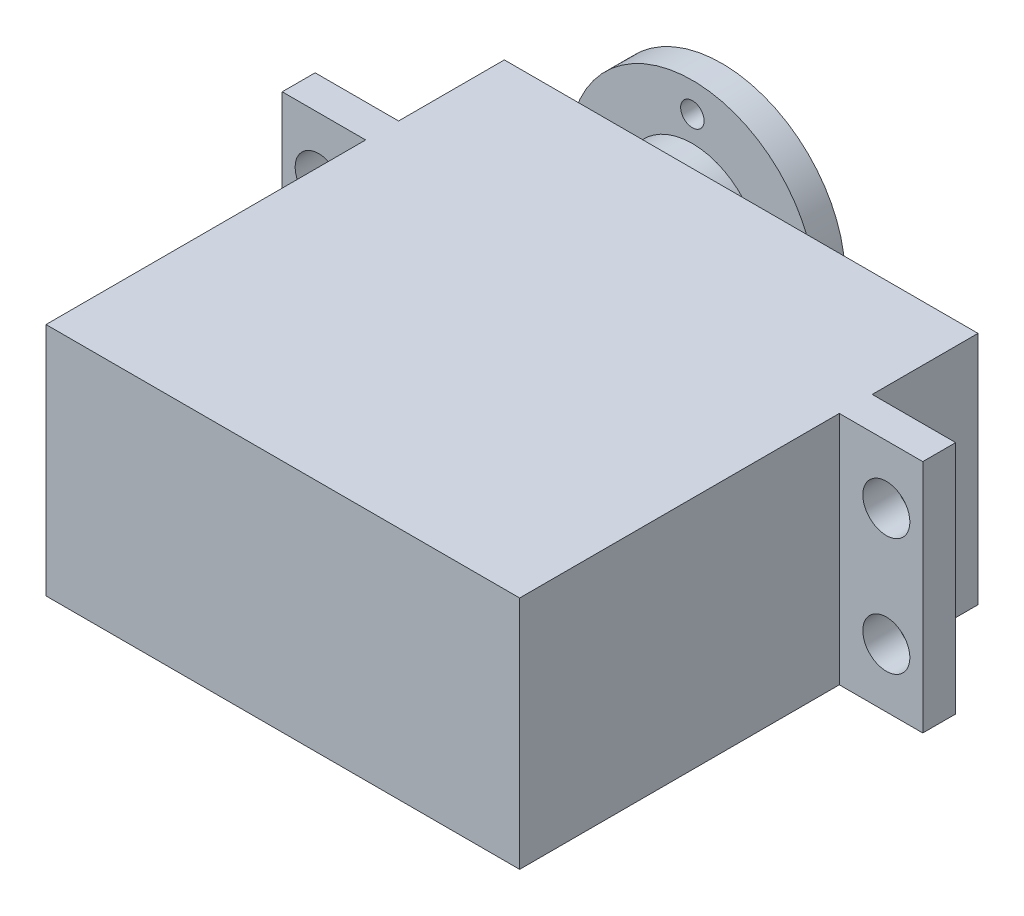
SolidWorks part; units mm, degrees
ref_plane "Alzado" through (0, 0, 0) normal (0, 0, 1) x (1, 0, 0)
ref_plane "Planta" through (0, 0, 0) normal (0, 1, 0) x (1, 0, 0)
ref_plane "Vista lateral" through (0, 0, 0) normal (1, 0, 0) x (0, 0, -1)
sketch "Croquis1" plane through (0, 0, 0) normal (0, 1, 0) x (1, 0, 0)
  line L0 (0, 19.5) -> (0, -19.5) construction
  line L1 (20.15, 19.5) -> (-20.15, 19.5)
  line L2 (20.15, -19.5) -> (20.15, 7.7)
  line L3 (20.15, -19.5) -> (-20.15, -19.5)
  line L4 (-20.15, -19.5) -> (-20.15, 7.7)
  line L5 (20.15, 19.5) -> (-20.15, -19.5) construction
  line L6 (20.15, -19.5) -> (-20.15, 19.5) construction
  line L7 (-20.15, 10.5) -> (-20.15, 19.5)
  line L8 (-20.15, 10.5) -> (-27.25, 10.5)
  line L9 (20.15, 10.5) -> (20.15, 19.5)
  line L10 (-20.15, 7.7) -> (-27.25, 7.7)
  line L11 (-27.25, 10.5) -> (-27.25, 7.7)
  line L12 (27.25, 10.5) -> (27.25, 7.7)
  line L13 (20.15, 7.7) -> (27.25, 7.7)
  line L14 (20.15, 10.5) -> (27.25, 10.5)
  point P0 (0, 0)
  point P16 (27.25, 9.1)
  dimension "D1" = 39
  dimension "D2" = 40.3
  dimension "D3" = 54.5
  dimension "D4" = 27.2
  dimension "D5" = 2.8
  dimension "D6" = 30
extrude "Saliente-Extruir1" add sketch "Croquis1" along normal blind 20
sketch "Croquis3" plane through (0, 0, -19.5) normal (0, 0, -1) x (-1, 0, 0)
  line L0 (-20.15, 10) -> (20.15, 10) construction
  line L1 (-20.15, 20) -> (-20.15, 0) construction
  line L2 (20.15, 20) -> (20.15, 0) construction
  circle A0 centre (10.15, 10) radius 5.8375
  dimension "D1" = 10
extrude "Saliente-Extruir3" add sketch "Croquis3" along normal blind 8.5
sketch "Croquis4" plane through (0, 0, -10.5) normal (0, 0, -1) x (-1, 0, 0)
  line L0 (0, 0) -> (0, 20) construction
  line L1 (-20.15, 20) -> (20.15, 20) construction
  line L2 (-27.25, 10) -> (27.25, 10) construction
  line L3 (-27.25, 20) -> (-27.25, 0) construction
  line L4 (27.25, 20) -> (27.25, 0) construction
  line L5 (-20.15, 20) -> (-20.15, 0) construction
  circle A0 centre (-24.15, 15) radius 2
  circle A1 centre (-24.15, 5) radius 2
  circle A2 centre (24.15, 5) radius 2
  circle A3 centre (24.15, 15) radius 2
  dimension "D2" = 4
  dimension "D1" = 10
  dimension "D3" = 4
extrude "Cortar-Extruir1" cut sketch "Croquis4" against normal blind 10
sketch "Croquis5" plane through (0, 0, -28) normal (0, 0, -1) x (-1, 0, 0)
  circle A0 centre (10.15, 10) radius 10.5
  dimension "D1" = 21
extrude "Saliente-Extruir4" add sketch "Croquis5" against normal blind 2.5
sketch "Croquis6" plane through (0, 0, -28) normal (0, 0, -1) x (-1, 0, 0)
  line L0 (10.15, 20.5) -> (10.15, -0.5) construction
  line L1 (-0.35, 10) -> (20.65, 10) construction
  circle A0 centre (10.15, 10) radius 10.5 construction
  circle A1 centre (10.15, 18) radius 1
  circle A2 centre (18.15, 10) radius 1
  circle A3 centre (2.15, 10) radius 1
  circle A4 centre (10.15, 2) radius 1
  point P15 (10.15, 10)
  dimension "D1" = 8
  dimension "D3" = 2
  dimension "D2" = 8
extrude "Cortar-Extruir3" cut sketch "Croquis6" against normal up to next
